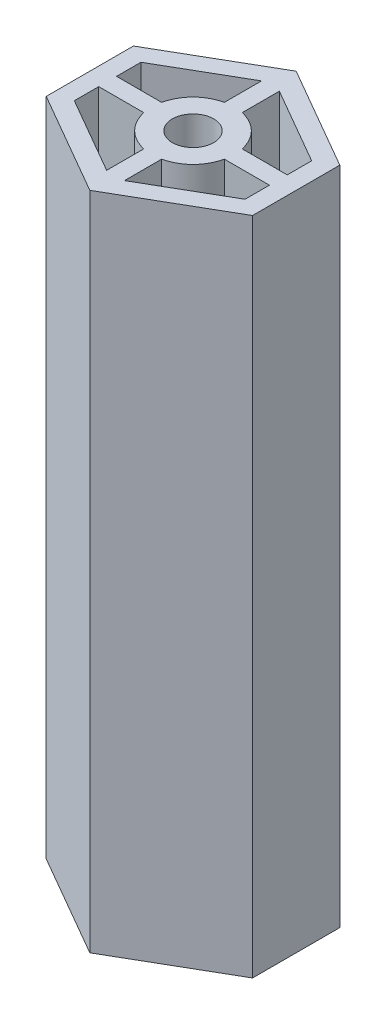
SolidWorks part; units mm, degrees
ref_plane "Front Plane" through (0, 0, 0) normal (0, 0, 1) x (1, 0, 0)
ref_plane "Top Plane" through (0, 0, 0) normal (0, 1, 0) x (1, 0, 0)
ref_plane "Right Plane" through (0, 0, 0) normal (1, 0, 0) x (0, 0, -1)
sketch "Sketch1" plane through (0, 0, 0) normal (0, 1, 0) x (1, 0, 0)
  line L0 (-12.5, 5.2831) -> (-12.5, -5.2831)
  line L1 (-12.5, 12.5) -> (12.5, 12.5) construction
  line L2 (-12.5, 12.5) -> (-12.5, -12.5) construction
  line L3 (-12.5, -12.5) -> (12.5, -12.5) construction
  line L4 (12.5, 12.5) -> (12.5, -12.5) construction
  line L5 (-12.5, -5.2831) -> (0, -12.5)
  line L6 (-12.5, 5.2831) -> (0, 12.5)
  line L7 (0, 4.0578) -> (0, -4.1758) construction
  line L8 (12.5, -5.2831) -> (0, -12.5)
  line L9 (12.5, 5.2831) -> (12.5, -5.2831)
  line L10 (12.5, 5.2831) -> (0, 12.5)
  line L11 (-1.08, 9.3823) -> (-1.08, 4.882)
  line L12 (1.08, 9.3823) -> (1.08, 4.882)
  line L13 (-10.34, 1.08) -> (-4.882, 1.08)
  line L14 (-10.34, -1.08) -> (-4.882, -1.08)
  line L15 (-1.08, -4.882) -> (-1.08, -9.3823)
  line L16 (1.08, -4.882) -> (1.08, -9.3823)
  line L17 (4.882, 1.08) -> (10.34, 1.08)
  line L18 (4.882, -1.08) -> (10.34, -1.08)
  line L19 (-10.34, 4.036) -> (-1.08, 9.3823)
  line L20 (10.34, 4.036) -> (1.08, 9.3823)
  line L21 (10.34, 4.036) -> (10.34, 1.08)
  line L22 (10.34, -4.036) -> (1.08, -9.3823)
  line L23 (-10.34, -4.036) -> (-1.08, -9.3823)
  line L24 (-10.34, 4.036) -> (-10.34, 1.08)
  line L25 (-10.34, -1.08) -> (-10.34, -4.036)
  line L26 (-10.34, 4.036) -> (-10.34, -4.036) construction
  line L27 (-10.34, -4.036) -> (0, -10.0058) construction
  line L28 (10.34, -4.036) -> (0, -10.0058) construction
  line L29 (10.34, -1.08) -> (10.34, -4.036)
  line L30 (10.34, 4.036) -> (10.34, -4.036) construction
  line L31 (-10.34, 4.036) -> (0, 10.0058) construction
  line L32 (10.34, 4.036) -> (0, 10.0058) construction
  arc A0 (-4.882, -1.08) -> (-1.08, -4.882) centre (0, 0) ccw
  circle A1 centre (0, 0) radius 2.5
  arc A2 (-1.08, 4.882) -> (-4.882, 1.08) centre (0, 0) ccw
  arc A3 (4.882, 1.08) -> (1.08, 4.882) centre (0, 0) ccw
  arc A4 (1.08, -4.882) -> (4.882, -1.08) centre (0, 0) ccw
  point P4 (-12.5, 0)
  point P5 (0, -12.5)
  point P13 (0, 12.5)
  dimension "D4" = 10
  dimension "D9" = 5
  dimension "D1" = 25
  dimension "D2" = 120
  dimension "D3" = 120
  dimension "D5" = 2.16
  dimension "D6" = 1.08
  dimension "D7" = 2.16
  dimension "D8" = 1.08
  dimension "D10" = 2.16
extrude "Boss-Extrude2" add sketch "Sketch1" along normal blind 80
equation "\"diameter\"= 4mm"
equation "\"D9@Sketch1\"=\"diameter\"+1mm"
equation "\"D4@Sketch1\"=(\"diameter\"+1mm)*2"
